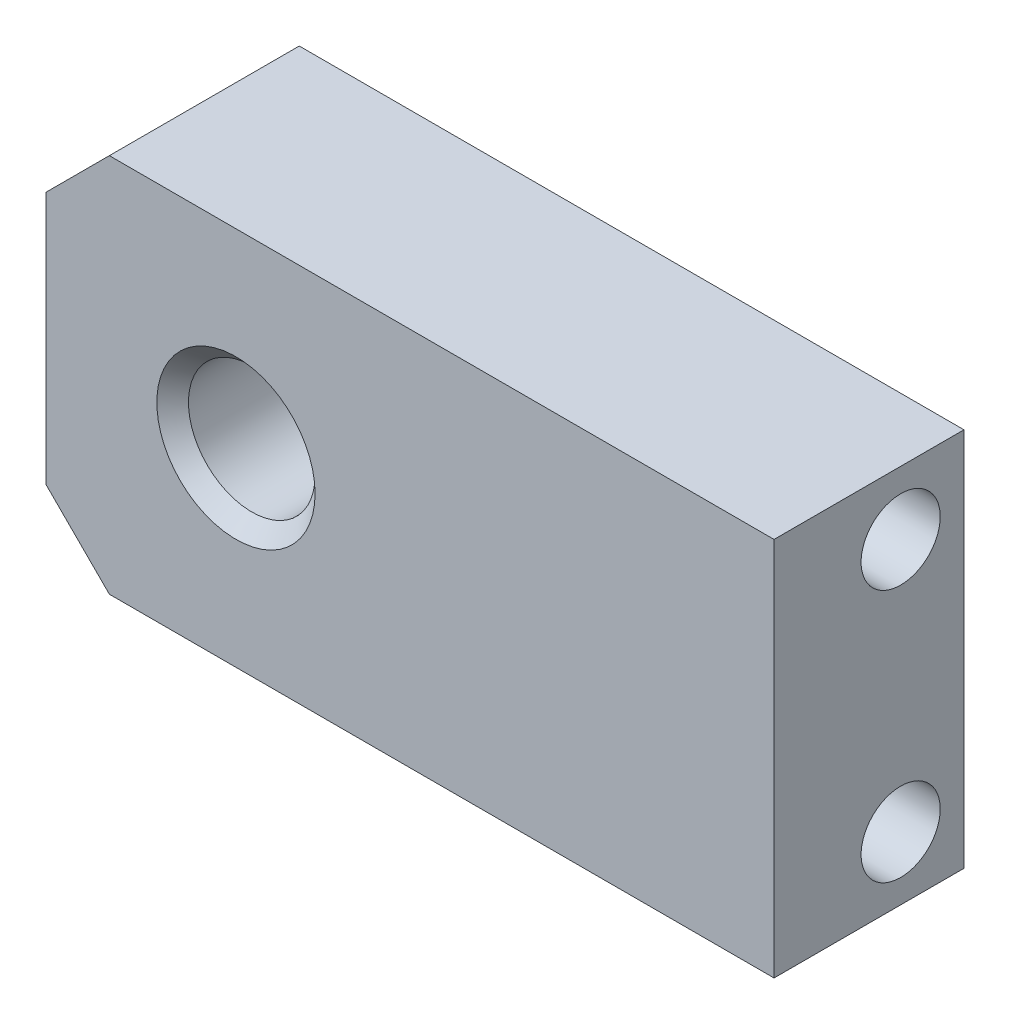
SolidWorks part; units mm, degrees
material "Brass"
ref_plane "Front Plane" through (0, 0, 0) normal (0, 0, 1) x (1, 0, 0)
ref_plane "Top Plane" through (0, 0, 0) normal (0, 1, 0) x (1, 0, 0)
ref_plane "Right Plane" through (0, 0, 0) normal (1, 0, 0) x (0, 0, -1)
sketch "Sketch5" plane through (0, 0, 0) normal (0, 0, 1) x (1, 0, 0)
  line L0 (-9.5, -6) -> (-11.5, -4)
  line L1 (-9.5, 6) -> (11.5, 6)
  line L2 (-11.5, 4) -> (-11.5, -4)
  line L3 (-9.5, -6) -> (11.5, -6)
  line L4 (11.5, 6) -> (11.5, -6)
  line L5 (-11.5, 6) -> (11.5, -6) construction
  line L6 (-11.5, -6) -> (11.5, 6) construction
  line L7 (-9.5, 6) -> (-11.5, 4)
  circle A0 centre (-5.5, 0) radius 2
  point P0 (0, 0)
  dimension "D7" = 4
  dimension "D1" = 23
  dimension "D2" = 12
  dimension "D3" = 2
  dimension "D4" = 2
  dimension "D5" = 2
  dimension "D6" = 2
  dimension "D8" = 17
extrude "Boss-Extrude3" add sketch "Sketch5" along normal blind 6
chamfer "Chamfer1" distance 0.5 angle 45 2 edges at (-3.5, 0, 6) (-3.5, 0, 0)
hole_wizard "M3x0.5 Tapped Hole2" positions "3DSketch1" profile "Sketch6" tap size "M3x0.5" standard "ANSI Metric"
sketch3d "3DSketch1"
  line L0 (11.5, -6, 6) -> (11.5, 6, 6) construction
  line L2 (11.5, 6, 6) -> (11.5, 6, 0) construction
  line L3 (11.5, -6, 6) -> (11.5, -6, 0) construction
  point P0 (11.5, 4, 2)
  point P2 (11.5, -4, 2)
  dimension "D1" = 4
  dimension "D2" = 4
  dimension "D3" = 2
  dimension "D4" = 2
sketch "Sketch6" plane through (11.5, 4, 2) normal (0, 1, 0) x (0, 0, -1)
  line L0 (0, 0) -> (0, 10.7511)
  line L1 (0, 10.7511) -> (1.25, 10)
  line L2 (1.25, 10) -> (1.25, 0)
  line L5 (1.25, 0) -> (0, 0)
  line L10 (0, 10.7511) -> (-1.25, 10) construction
  line L11 (0, -6.35) -> (0, 107.95) construction
  dimension "Tap Drill Dia." = 2.5
  dimension "Tap Drill Depth" = 10
  dimension "Drill Angle" = 118
cosmetic thread "Hole Thread1" parameters "D1"=8, "D2"=3
cosmetic thread "Hole Thread2" parameters "D1"=8, "D2"=3
